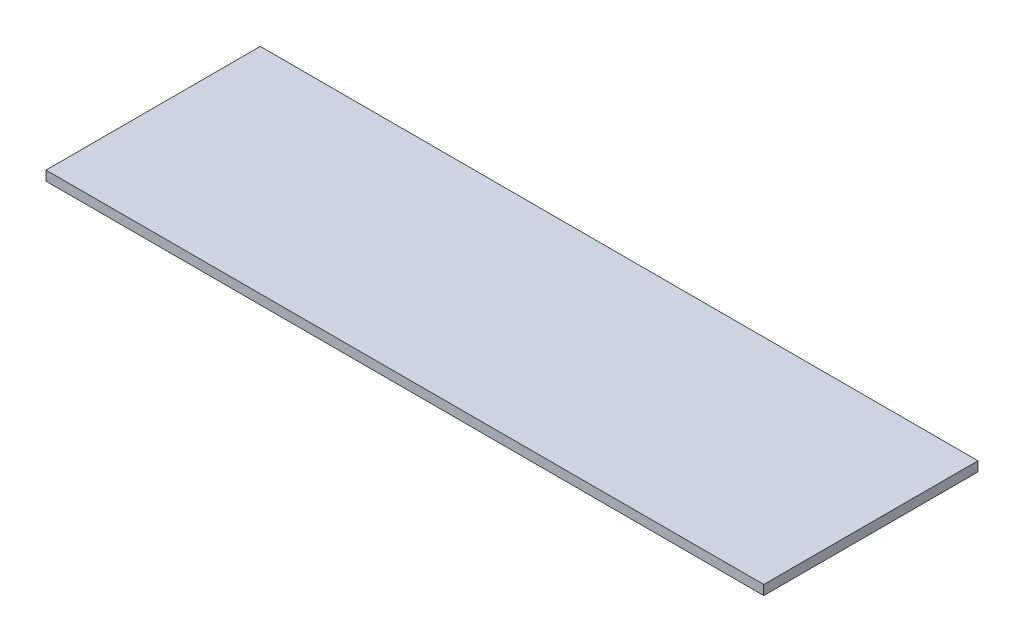
SolidWorks part; units mm, degrees
ref_plane "Front Plane" through (0, 0, 0) normal (0, 0, 1) x (1, 0, 0)
ref_plane "Top Plane" through (0, 0, 0) normal (0, 1, 0) x (1, 0, 0)
ref_plane "Right Plane" through (0, 0, 0) normal (1, 0, 0) x (0, 0, -1)
sketch "Sketch1" plane through (0, 0, 0) normal (0, 1, 0) x (1, 0, 0)
  line L1 (0, 0) -> (1340, 0)
  line L2 (0, 0) -> (0, 400)
  line L3 (0, 400) -> (1340, 400)
  line L4 (1340, 0) -> (1340, 400)
  dimension "D1" = 400
  dimension "D2" = 1340
extrude "Boss-Extrude1" add sketch "Sketch1" along normal blind 18
